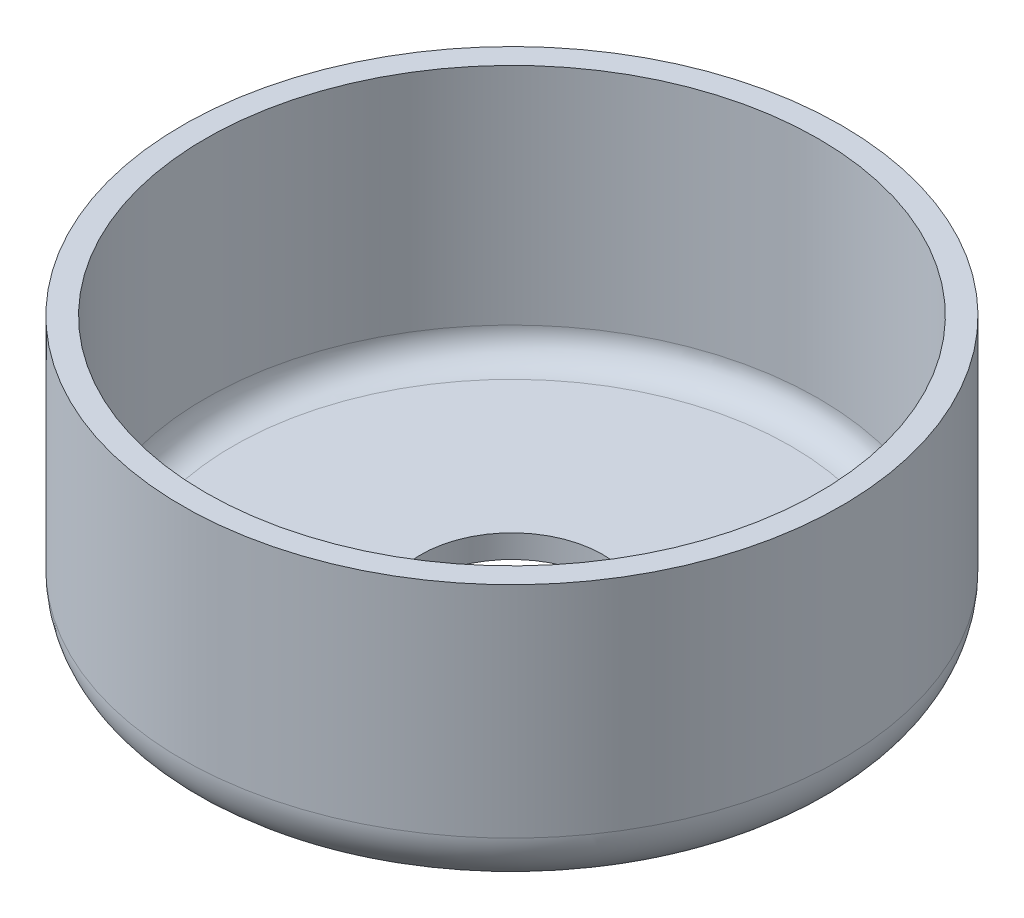
SolidWorks part; units mm, degrees
material "Copper"
ref_plane "Front Plane" through (0, 0, 0) normal (0, 0, 1) x (1, 0, 0)
ref_plane "Top Plane" through (0, 0, 0) normal (0, 1, 0) x (1, 0, 0)
ref_plane "Right Plane" through (0, 0, 0) normal (1, 0, 0) x (0, 0, -1)
sketch "Sketch1" plane through (0, 0, 0) normal (0, 0, 1) x (1, 0, 0)
  line L0 (3.302, 0) -> (9.9314, 0)
  line L1 (11.9634, 2.032) -> (11.9634, 10)
  line L2 (0, 0) -> (0, 16.4584) construction
  line L3 (11.1252, 10) -> (11.9634, 10)
  line L4 (3.302, 0) -> (3.302, 0.8382)
  line L5 (3.302, 0.8382) -> (10.1252, 0.8382)
  line L6 (11.1252, 1.8382) -> (11.1252, 10)
  arc A0 (9.9314, 0) -> (11.9634, 2.032) centre (9.9314, 2.032) ccw
  arc A1 (10.1252, 0.8382) -> (11.1252, 1.8382) centre (10.1252, 1.8382) ccw
  dimension "D1" = 2.032
  dimension "D5" = 1
  dimension "D2" = 3.302
  dimension "D3" = 10
  dimension "D4" = 11.9634
  dimension "D6" = 0.8382
  dimension "D7" = 0.8382
revolve "Revolve1" add sketch "Sketch1" angle 360 about L2
sketch "Sketch2" plane through (0, 0, 0) normal (0, 0, 1) x (1, 0, 0)
  line L0 (0, 2.032) -> (0, 0) construction
  line L1 (-0.7938, 12.7727) -> (0.7937, 12.7727)
  line L2 (-0.7938, 12.7727) -> (-0.7937, 2.032)
  line L3 (-0.7937, 2.032) -> (0.7937, 2.032)
  line L4 (0.7937, 12.7727) -> (0.7937, 2.032)
  line L5 (11.9634, 2.032) -> (-11.9634, 2.032) construction
  dimension "D1" = 1.5875
extrude "Cut-Extrude1" [suppressed] cut sketch "Sketch2" against normal through all
pattern_circular "CirPattern1" [suppressed] count 12 over 360
